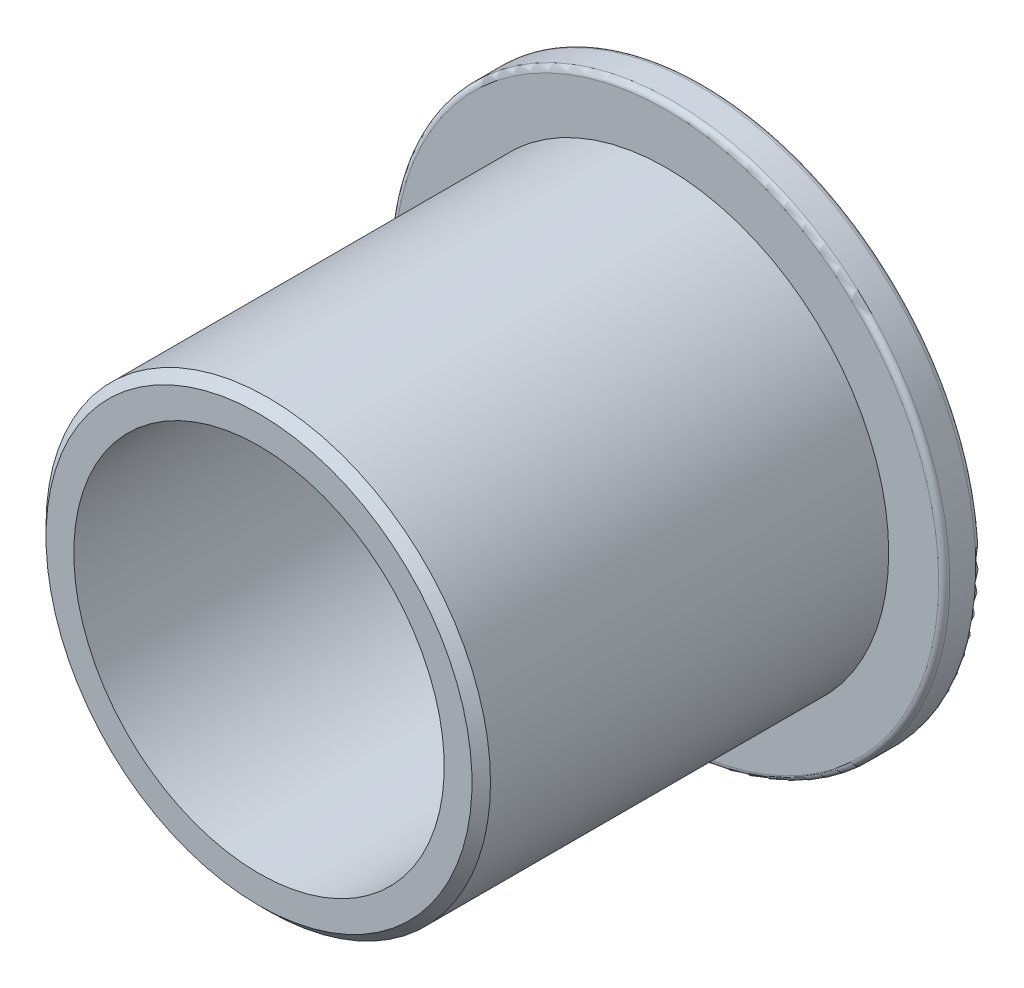
SolidWorks part; units mm, degrees
material "PA Type 6"
ref_plane "Front Plane" through (0, 0, 0) normal (0, 0, 1) x (1, 0, 0)
ref_plane "Top Plane" through (0, 0, 0) normal (0, 1, 0) x (1, 0, 0)
ref_plane "Right Plane" through (0, 0, 0) normal (1, 0, 0) x (0, 0, -1)
sketch "Sketch1" plane through (0, 0, 0) normal (1, 0, 0) x (0, 0, -1)
  line L0 (-9.525, 0) -> (9.525, 0) construction
  line L1 (9.525, 11.9063) -> (9.525, -11.9062) construction
  line L2 (-9.525, 9.525) -> (-9.525, -9.525) construction
  line L3 (9.525, 11.9063) -> (7.9375, 11.9062) construction
  line L4 (9.525, -11.9062) -> (7.9375, -11.9062) construction
  point P2 (0, 0)
  point P7 (-9.525, 0)
  point P8 (-9.525, -7.9375)
  point P9 (9.525, 0)
  point P11 (-9.525, 7.9375)
  dimension "Flange OD" = 23.8125
  dimension "OD" = 19.05
  dimension "ID" = 15.875
  dimension "Length" = 19.05
  dimension "Flange Thickness" = 1.5875
sketch "Sketch2" plane through (0, 0, 0) normal (0, 0, 1) x (1, 0, 0)
  line L0 (-11.9063, 0) -> (11.9063, 0) construction
  line L1 (0, -11.9063) -> (0, 11.9063) construction
  circle A0 centre (0, 0) radius 7.9375 construction
  circle A1 centre (0, 0) radius 9.525 construction
  circle A2 centre (0, 0) radius 11.9063 construction
  dimension "ID" = 15.875
  dimension "OD" = 19.05
  dimension "Flange OD" = 23.8125
sketch "Sketch3" plane through (0, 0, 0) normal (1, 0, 0) x (0, 0, -1)
  line L0 (-9.525, 7.9375) -> (9.525, 7.9375)
  line L1 (9.525, 11.9063) -> (9.525, -11.9062) construction
  line L2 (9.525, 7.9375) -> (9.525, 11.9063)
  line L3 (9.525, 11.9063) -> (7.9375, 11.9062)
  line L4 (7.9375, 11.9062) -> (7.9375, 9.525)
  line L5 (7.9375, 9.525) -> (-9.525, 9.525)
  line L6 (-9.525, 9.525) -> (-9.525, 7.9375)
  line L7 (-9.525, 0) -> (9.525, 0) construction
revolve "Revolve1" add sketch "Sketch3" angle 360 about L7
chamfer "Chamfer1" distance 0.3969 angle 45 1 edges at (0, -9.525, 9.525)
fillet "Fillet1" [suppressed] radius 0.381
fillet "Fillet2" radius 0.2381 2 edges at (0, -11.9062, -9.525) (0, -11.9062, -7.9375)
chamfer "Chamfer2" distance 0.7937 angle 45 1 edges at (0, -7.9375, -9.525)
equation "\"D1@Chamfer1\"=((\"OD@Sketch1\"-\"ID@Sketch1\")/2)*.25"
equation "\"D1@Fillet1\"=\"OD@Sketch1\"*.02"
equation "\"D1@Fillet2\"=\"Flange OD@Sketch1\"*.01"
equation "\"D1@Chamfer2\"=\"ID@Sketch1\"*.05"
